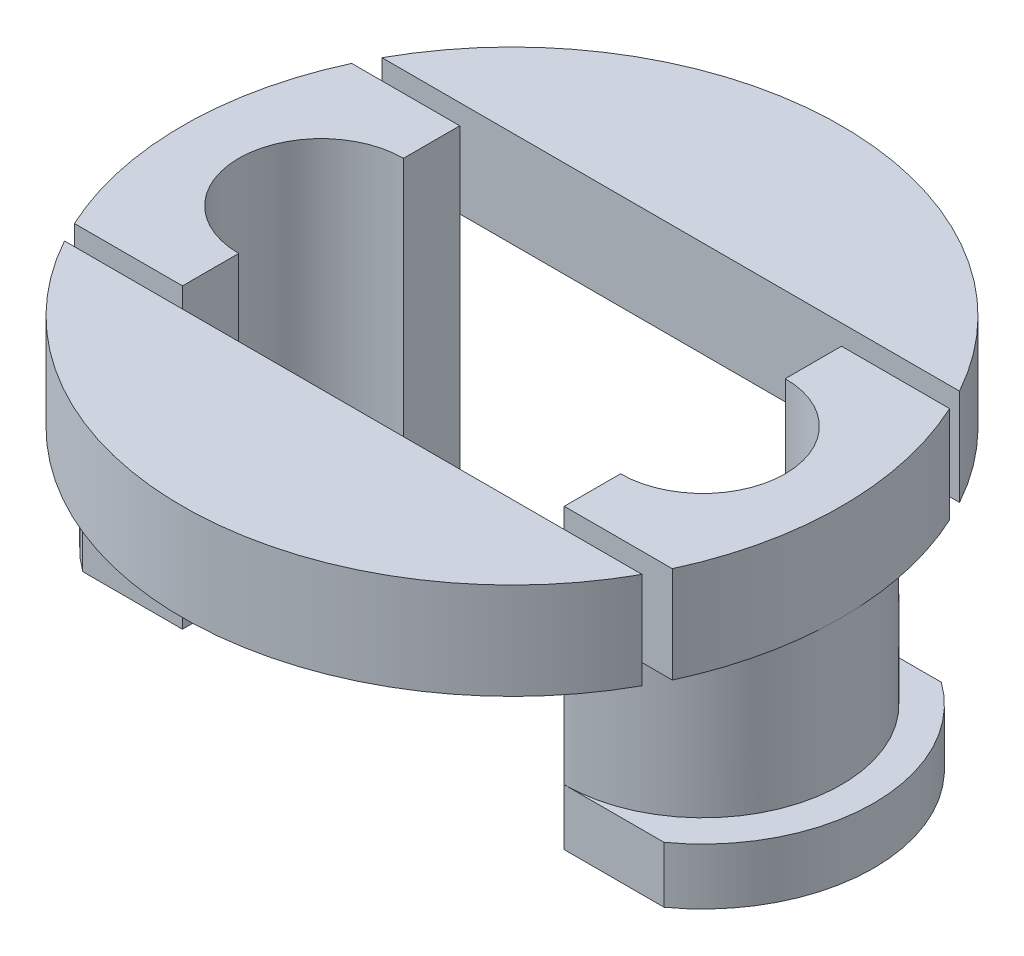
SolidWorks part; units mm, degrees
ref_plane "正面" through (0, 0, 0) normal (0, 0, 1) x (1, 0, 0)
ref_plane "平面" through (0, 0, 0) normal (0, 1, 0) x (1, 0, 0)
ref_plane "右側面" through (0, 0, 0) normal (1, 0, 0) x (0, 0, -1)
sketch "ｽｹｯﾁ1" plane through (0, 0, 0) normal (0, 1, 0) x (1, 0, 0)
  line L0 (-10.2, 0) -> (10.2, 0) construction
  line L1 (-5.6, 0) -> (3.9, 0) construction
  line L2 (-5.6, 3.55) -> (3.9, 3.55) construction
  line L3 (-5.6, -3.55) -> (3.9, -3.55) construction
  line L4 (-5.6, 3.45) -> (3.9, 3.45)
  line L5 (-5.6, -3.45) -> (3.9, -3.45)
  line L6 (-5.6, 2.05) -> (3.9, 2.05)
  line L7 (-5.6, -2.05) -> (3.9, -2.05)
  arc A0 (-5.6, 3.55) -> (-5.6, -3.55) centre (-5.6, 0) ccw construction
  arc A1 (3.9, -3.55) -> (3.9, 3.55) centre (3.9, 0) ccw construction
  arc A2 (3.9, -3.45) -> (3.9, 3.45) centre (3.9, 0) ccw
  arc A3 (-5.6, 3.45) -> (-5.6, -3.45) centre (-5.6, 0) ccw
  arc A4 (3.9, -2.05) -> (3.9, 2.05) centre (3.9, 0) ccw
  arc A5 (-5.6, 2.05) -> (-5.6, -2.05) centre (-5.6, 0) ccw
  point P4 (-0.85, 0)
  dimension "D1" = 7.1
  dimension "D2" = 9.5
  dimension "D3" = 0.1
  dimension "D4" = 1.5
extrude "ﾎﾞｽ - 押し出し1" add sketch "ｽｹｯﾁ1" along normal blind 4
sketch "ｽｹｯﾁ2" plane through (0, 4, 0) normal (0, 1, 0) x (1, 0, 0)
  line L0 (-0.85, 2.05) -> (-0.85, -2.05) construction
  line L6 (-5.6, -2.05) -> (3.9, -2.05)
  line L7 (3.9, 2.05) -> (-5.6, 2.05)
  line L8 (-5.6, -2.05) -> (3.9, -2.05)
  line L9 (3.9, 2.05) -> (-5.6, 2.05)
  circle A0 centre (-0.85, 0) radius 8.2
  arc A6 (3.9, -2.05) -> (3.9, 2.05) centre (3.9, 0) ccw
  arc A7 (-5.6, 2.05) -> (-5.6, -2.05) centre (-5.6, 0) ccw
  arc A8 (3.9, -2.05) -> (3.9, 2.05) centre (3.9, 0) ccw
  arc A9 (-5.6, 2.05) -> (-5.6, -2.05) centre (-5.6, 0) ccw
  dimension "D1" = 16.4
  dimension "D2" = 0
extrude "ﾎﾞｽ - 押し出し2" add sketch "ｽｹｯﾁ2" along normal blind 2.4
sketch "ｽｹｯﾁ3" plane through (0, 0, 0) normal (0, -1, 0) x (1, 0, 0)
  line L0 (-5.6, 2.05) -> (3.9, 2.05) construction
  line L2 (3.9, -2.05) -> (-5.6, -2.05) construction
  line L4 (-5.6, -3.45) -> (3.9, -3.45)
  line L5 (3.9, 3.45) -> (-5.6, 3.45)
  line L6 (-5.6, -3.45) -> (3.9, -3.45)
  line L7 (3.9, 3.45) -> (-5.6, 3.45)
  line L8 (-5.6, 2.05) -> (3.9, 2.05)
  line L9 (3.9, -2.05) -> (-5.6, -2.05)
  arc A0 (-5.6, 2.05) -> (-5.6, -2.05) centre (-5.6, 0) ccw construction
  arc A1 (3.9, -2.05) -> (3.9, 2.05) centre (3.9, 0) ccw construction
  arc A2 (-5.6, 3.45) -> (-5.6, -3.45) centre (-5.6, 0) ccw
  arc A3 (3.9, -3.45) -> (3.9, 3.45) centre (3.9, 0) ccw
  arc A4 (-5.6, 3.45) -> (-5.6, -3.45) centre (-5.6, 0) ccw
  arc A5 (3.9, -3.45) -> (3.9, 3.45) centre (3.9, 0) ccw
  arc A6 (-5.6, 2.05) -> (-5.6, -2.05) centre (-5.6, 0) ccw
  arc A7 (3.9, -2.05) -> (3.9, 2.05) centre (3.9, 0) ccw
  dimension "D1" = 0
extrude "ﾎﾞｽ - 押し出し3" add sketch "ｽｹｯﾁ3" along normal blind 1
sketch "ｽｹｯﾁ4" plane through (0, -1, 0) normal (0, -1, 0) x (1, 0, 0)
  line L0 (-9.05, 0) -> (-9.05, 2.5274) construction
  line L1 (7.35, 0) -> (10.3816, 0) construction
  line L2 (-0.85, 0) -> (-4.1643, 0) construction
  line L3 (7.35, 0) -> (7.35, 2.5274) construction
  line L4 (-0.85, 1.75) -> (-0.85, -1.75) construction
  line L5 (-9.05, 0) -> (-12.0816, 0) construction
  line L6 (3.9, -3.45) -> (6.3819, -3.45)
  line L7 (3.9, 3.45) -> (6.3819, 3.45)
  line L10 (-5.6, 3.45) -> (-8.0819, 3.45)
  line L11 (-5.6, -3.45) -> (-8.0819, -3.45)
  line L21 (7.35, 0) -> (10.3816, 0) construction
  arc A0 (6.3819, 3.45) -> (6.3819, -3.45) centre (3.9, 0) cw
  arc A1 (-5.6, 3.45) -> (-5.6, -3.45) centre (-5.6, 0) ccw construction
  arc A2 (-5.6, 3.45) -> (-5.6, -3.45) centre (-5.6, 0) ccw
  arc A3 (-8.0819, 3.45) -> (-8.0819, -3.45) centre (-5.6, 0) ccw
  arc A4 (3.9, 3.45) -> (3.9, -3.45) centre (3.9, 0) cw
  arc A5 (-5.6, 4.25) -> (-5.6, -4.25) centre (-5.6, 0) ccw construction
extrude "ﾎﾞｽ - 押し出し4" add sketch "ｽｹｯﾁ4" against normal blind 1.4
sketch "ｽｹｯﾁ10" plane through (0, 6.4, 0) normal (0, 1, 0) x (1, 0, 0)
  line L0 (3.9, 2.05) -> (-5.6, 2.05) construction
  line L1 (-5.6, -2.05) -> (3.9, -2.05) construction
  line L2 (3.9, 2.05) -> (-5.6, 2.05)
  line L3 (-5.6, -2.05) -> (3.9, -2.05)
  line L5 (-19.35, -15.05) -> (-19.35, 15.05)
  line L6 (-19.35, -15.05) -> (17.65, -15.05)
  line L7 (17.65, -15.05) -> (17.65, 15.05)
  line L8 (-19.35, 15.05) -> (17.65, 15.05)
  arc A0 (-5.6, 2.05) -> (-5.6, -2.05) centre (-5.6, 0) ccw construction
  circle A1 centre (-0.85, 0) radius 8.2
  circle A2 centre (-0.85, 0) radius 8.2 construction
  arc A3 (3.9, -2.05) -> (3.9, 2.05) centre (3.9, 0) ccw construction
  arc A4 (-5.6, 2.05) -> (-5.6, -2.05) centre (-5.6, 0) ccw
  arc A5 (3.9, -2.05) -> (3.9, 2.05) centre (3.9, 0) ccw
  dimension "D2" = 15.05
  dimension "D3" = 15.05
  dimension "D4" = 18.5
  dimension "D5" = 18.5
  dimension "D1" = 0
sketch "ｽｹｯﾁ12" plane through (0, -1, 0) normal (0, -1, 0) x (1, 0, 0)
  line L0 (-0.85, 3.45) -> (-0.85, -3.45) construction
  line L3 (-5.1, 3.95) -> (-5.1, -3.95)
  line L4 (-5.6, 3.45) -> (-14.4592, 3.45)
  line L5 (-5.6, 3.45) -> (-5.6, -3.45)
  line L6 (-5.6, -3.45) -> (-14.4592, -3.45)
  line L7 (12.7592, 3.45) -> (12.7592, 3.95)
  line L8 (-5.1, -3.95) -> (-14.4592, -3.95)
  line L9 (3.4, 3.95) -> (12.7592, 3.95)
  line L10 (-5.1, 3.95) -> (-14.4592, 3.95)
  line L11 (-14.4592, 3.45) -> (-14.4592, 3.95)
  line L12 (-14.4592, -3.45) -> (-14.4592, -3.95)
  line L13 (-5.1, -3.95) -> (-14.9592, -3.95) construction
  line L14 (-5.1, 3.95) -> (-14.9592, 3.95) construction
  line L15 (-14.9592, 3.95) -> (-14.9592, -3.95) construction
  line L16 (-14.4592, 3.45) -> (-14.4592, -3.45) construction
  line L17 (3.4, -3.95) -> (12.7592, -3.95)
  line L18 (3.9, -3.45) -> (12.7592, -3.45)
  line L19 (3.9, 3.45) -> (3.9, -3.45)
  line L20 (3.9, 3.45) -> (12.7592, 3.45)
  line L21 (3.4, 3.95) -> (3.4, -3.95)
  line L22 (12.7592, -3.45) -> (12.7592, -3.95)
  dimension "D1" = 0.5
extrude "ｶｯﾄ - 押し出し1" cut sketch "ｽｹｯﾁ12" against normal up to surface (7.4 mm away) up to face at (-0.85, 6.4, 8.2)
sketch "ｽｹｯﾁ13" plane through (0, -1, 0) normal (0, -1, 0) x (1, 0, 0)
  line L1 (-5.1, 3.95) -> (3.4, 3.95)
  line L2 (-5.1, 3.95) -> (-5.1, 2.05)
  line L3 (-5.1, 2.05) -> (3.4, 2.05)
  line L4 (3.4, 3.95) -> (3.4, 2.05)
  line L5 (-5.1, -2.05) -> (3.4, -2.05)
  line L6 (-5.1, -2.05) -> (-5.1, -3.95)
  line L7 (-5.1, -3.95) -> (3.4, -3.95)
  line L8 (3.4, -2.05) -> (3.4, -3.95)
extrude "ｶｯﾄ - 押し出し2" cut sketch "ｽｹｯﾁ13" against normal up to surface (7.4 mm away) up to face at (-0.85, 6.4, -4.025)
